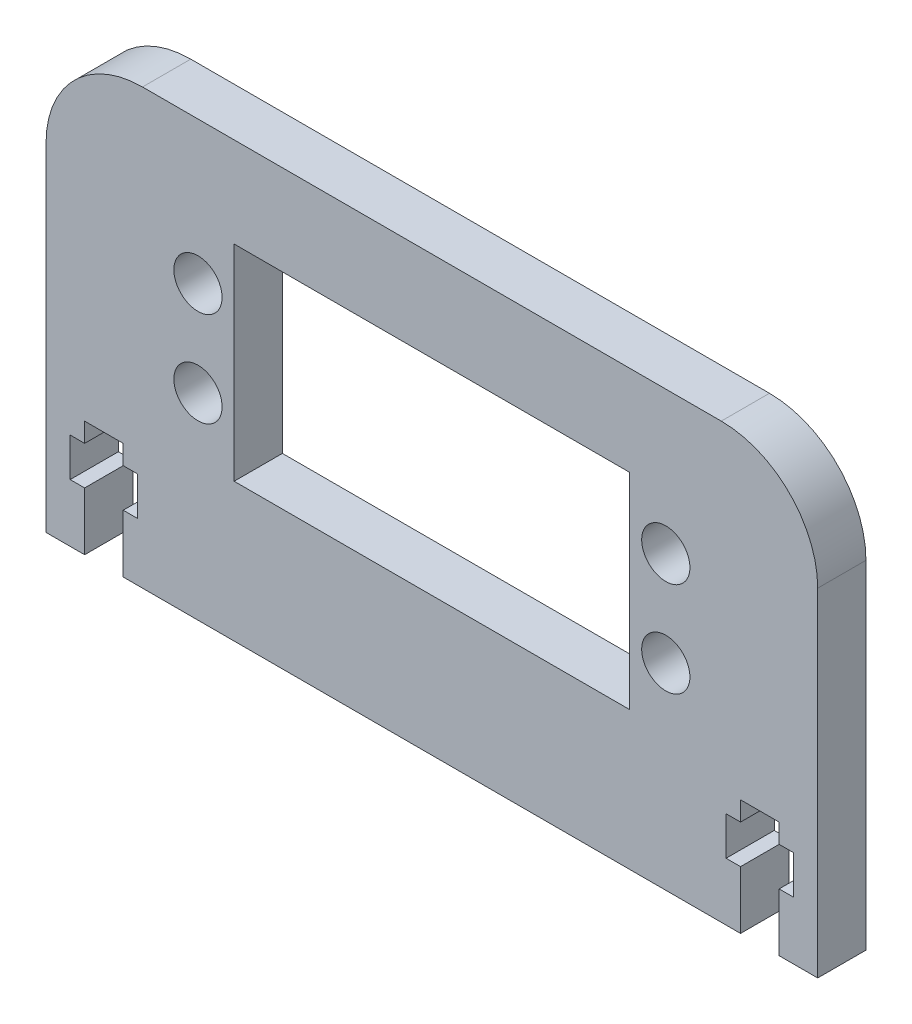
SolidWorks part; units mm, degrees
ref_plane "Front Plane" through (0, 0, 0) normal (0, 0, 1) x (1, 0, 0)
ref_plane "Top Plane" through (0, 0, 0) normal (0, 1, 0) x (1, 0, 0)
ref_plane "Right Plane" through (0, 0, 0) normal (1, 0, 0) x (0, 0, -1)
sketch "Sketch1" plane through (0, 0, 0) normal (0, 0, 1) x (1, 0, 0)
  line L0 (0, 22.5) -> (0, -22.5) construction
  line L1 (40, -22.5) -> (-40, -22.5)
  line L2 (40, -22.5) -> (40, 22.5)
  line L3 (40, 22.5) -> (-40, 22.5)
  line L4 (-40, -22.5) -> (-40, 22.5)
  line L5 (40, -22.5) -> (-40, 22.5) construction
  line L6 (40, 22.5) -> (-40, -22.5) construction
  point P0 (0, 0)
  dimension "D1" = 45
  dimension "D2" = 80
extrude "Boss-Extrude1" add sketch "Sketch1" along normal blind 5
sketch "Sketch2" plane through (0, 0, 5) normal (0, 0, 1) x (1, 0, 0)
  line L0 (-40, -22.5) -> (40, -22.5) construction
  line L12 (-40, 2.5) -> (40, 2.5) construction
  point P20 (0, 2.5)
  line B0 (-15, 2.5) -> (15, 2.5) construction
  line B1 (-30, 2.5) -> (30, 2.5) construction
  line B2 (-20.5, -8.15) -> (-20.5, 13.15)
  line B3 (-20.5, -8.15) -> (20.5, -8.15)
  line B4 (20.5, -8.15) -> (20.5, 13.15)
  line B5 (-20.5, 13.15) -> (20.5, 13.15)
  line B6 (-20.5, -8.15) -> (20.5, 13.15) construction
  line B7 (20.5, -8.15) -> (-20.5, 13.15) construction
  circle B8 centre (10.15, 2.5) radius 1.25 construction
  circle B9 centre (-24.25, -2.1) radius 2.5
  circle B10 centre (-24.25, 7.7237) radius 2.5
  circle B11 centre (24.25, 7.7237) radius 2.5
  circle B12 centre (24.25, -2.1) radius 2.5
  dimension "D1" = 25
sketch_block_instance "Block3-1"
sketch_block "Block3" parameters "D1"=2.5, "D2"=3.75, "D3"=10.15, "D4"=41, "D5"=41, "D6"=3.75, "D7"=21.3
extrude "Cut-Extrude1" cut sketch "Sketch2" against normal blind 10
sketch "Sketch3" plane through (0, 0, 5) normal (0, 0, 1) x (1, 0, 0)
  line L0 (-34, 23.4619) -> (-34, -20.0976) construction
  line L1 (-40, -22.5) -> (40, -22.5) construction
  line L2 (0, 22.5) -> (0, -22.5) construction
  line L3 (40, 22.5) -> (-40, 22.5) construction
  line B0 (-36, -22.5) -> (-32, -22.5)
  line B1 (-36, -16.5) -> (-36, -22.5)
  line B2 (-37.5, -16.5) -> (-36, -16.5)
  line B3 (-37.5, -12.5) -> (-37.5, -16.5)
  line B4 (-36, -12.5) -> (-37.5, -12.5)
  line B5 (-36, -10.5) -> (-36, -12.5)
  line B6 (-32, -10.5) -> (-36, -10.5)
  line B7 (-32, -12.5) -> (-32, -10.5)
  line B8 (-30.5, -12.5) -> (-32, -12.5)
  line B9 (-30.5, -16.5) -> (-30.5, -12.5)
  line B10 (-32, -16.5) -> (-30.5, -16.5)
  line B11 (-32, -22.5) -> (-32, -16.5)
  line B12 (-34, -22.5) -> (-34, -10.5)
  line B13 (36, -22.5) -> (32, -22.5)
  line B14 (36, -16.5) -> (36, -22.5)
  line B15 (37.5, -16.5) -> (36, -16.5)
  line B16 (37.5, -12.5) -> (37.5, -16.5)
  line B17 (36, -12.5) -> (37.5, -12.5)
  line B18 (36, -10.5) -> (36, -12.5)
  line B19 (32, -10.5) -> (36, -10.5)
  line B20 (32, -12.5) -> (32, -10.5)
  line B21 (30.5, -12.5) -> (32, -12.5)
  line B22 (30.5, -16.5) -> (30.5, -12.5)
  line B23 (32, -16.5) -> (30.5, -16.5)
  line B24 (32, -22.5) -> (32, -16.5)
  line B25 (34, -22.5) -> (34, -10.5)
  line M25 (-40, -22.5) -> (40, -22.5)
  dimension "D1" = 34
sketch_block_instance "Block2-1"
sketch_block "Block2" parameters "D1"=4
sketch_block_instance "Block2-2"
extrude "Cut-Extrude2" cut sketch "Sketch3" against normal blind 10 contours B12 B6 B5 B4 B3 B2 B1 M25 | B12 B0 B11 B10 B9 B8 B7 B6 | B25 B19 B20 B21 B22 B23 B24 M25 | B25 B13 B14 B15 B16 B17 B18 B19
fillet "Fillet1" radius 10 2 edges at (40, 22.5, 2.5) (-40, 22.5, 2.5)
